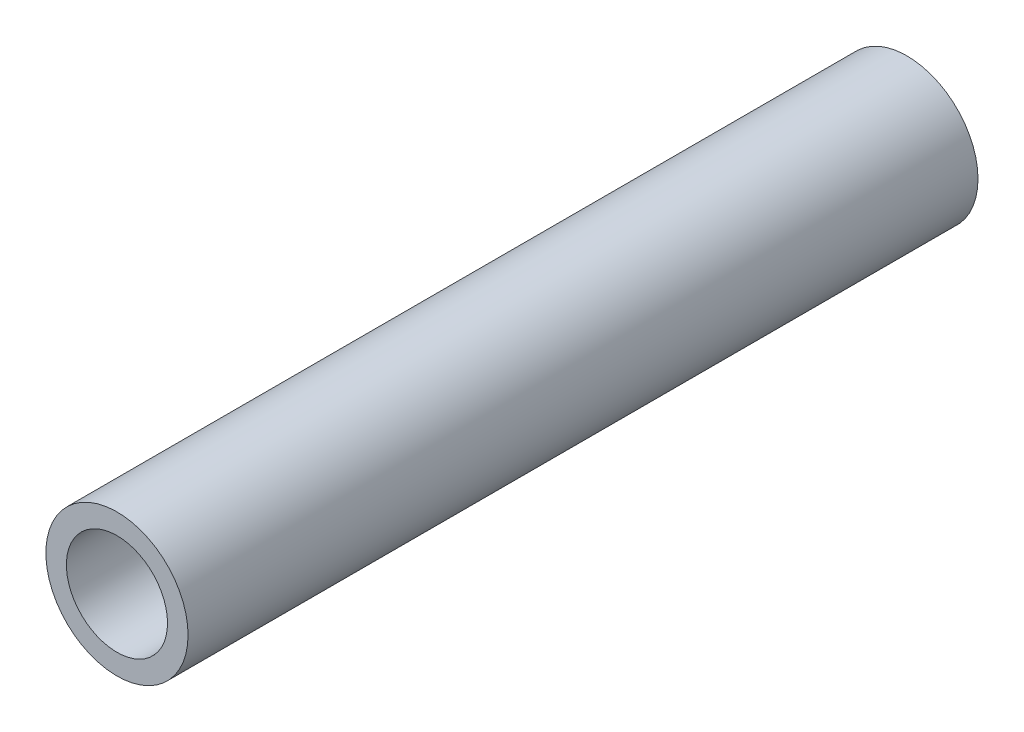
SolidWorks part; units mm, degrees
ref_plane "Front Plane" through (0, 0, 0) normal (0, 0, 1) x (1, 0, 0)
ref_plane "Top Plane" through (0, 0, 0) normal (0, 1, 0) x (1, 0, 0)
ref_plane "Right Plane" through (0, 0, 0) normal (1, 0, 0) x (0, 0, -1)
sketch "Sketch1" plane through (0, 0, 0) normal (0, 0, 1) x (1, 0, 0)
  circle A0 centre (0, 0) radius 2.25
  circle A1 centre (0, 0) radius 1.6
  dimension "OD" = 4.5
  dimension "ID" = 3.2
extrude "Extrude1" add sketch "Sketch1" along normal mid plane 25
sketch "Sketch2" plane through (0, 0, 0) normal (1, 0, 0) x (0, 0, -1)
  line L0 (-12.5, -1.6) -> (12.5, -1.6) construction
  line L3 (12.5, 1.6) -> (-12.5, 1.6) construction
  line L5 (-12.5, -1.6) -> (12.5, -1.6)
  line L6 (12.5, 1.6) -> (-12.5, 1.6)
sketch "Sketch4" plane through (0, 0, 12.5) normal (0, 0, 1) x (1, 0, 0)
  line L0 (0, 0) -> (-1.1314, 1.1314)
  line L1 (0, -55) -> (0, 55) construction
  circle A0 centre (0, 0) radius 1.6 construction
  dimension "D1" = 45
